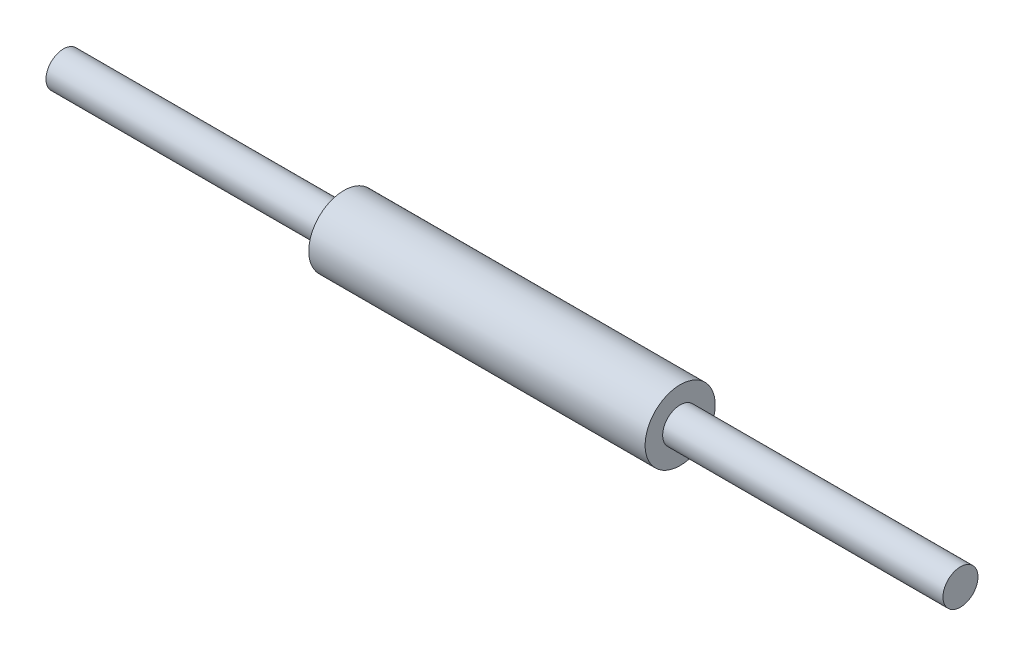
SolidWorks part; units mm, degrees
ref_plane "Front Plane" through (0, 0, 0) normal (0, 0, 1) x (1, 0, 0)
ref_plane "Top Plane" through (0, 0, 0) normal (0, 1, 0) x (1, 0, 0)
ref_plane "Right Plane" through (0, 0, 0) normal (1, 0, 0) x (0, 0, -1)
sketch "Sketch2" plane through (0, 0, 0) normal (1, 0, 0) x (0, 0, -1)
  circle A0 centre (0, 0) radius 12.5
  dimension "D1" = 25
extrude "Boss-ExtrudeAB" add sketch "Sketch2" along normal blind 200
sketch "Sketch3" plane through (200, 0, 0) normal (1, 0, 0) x (0, 0, -1)
  circle A0 centre (0, 0) radius 25
  dimension "D1" = 50
extrude "Boss-ExtrudeBC" add sketch "Sketch3" along normal blind 240 separate body
sketch "Sketch4" plane through (440, 0, 0) normal (1, 0, 0) x (0, 0, -1)
  circle A0 centre (0, 0) radius 12.5
  dimension "D1" = 25
extrude "Boss-ExtrudeCD" add sketch "Sketch4" along normal blind 200 separate body
